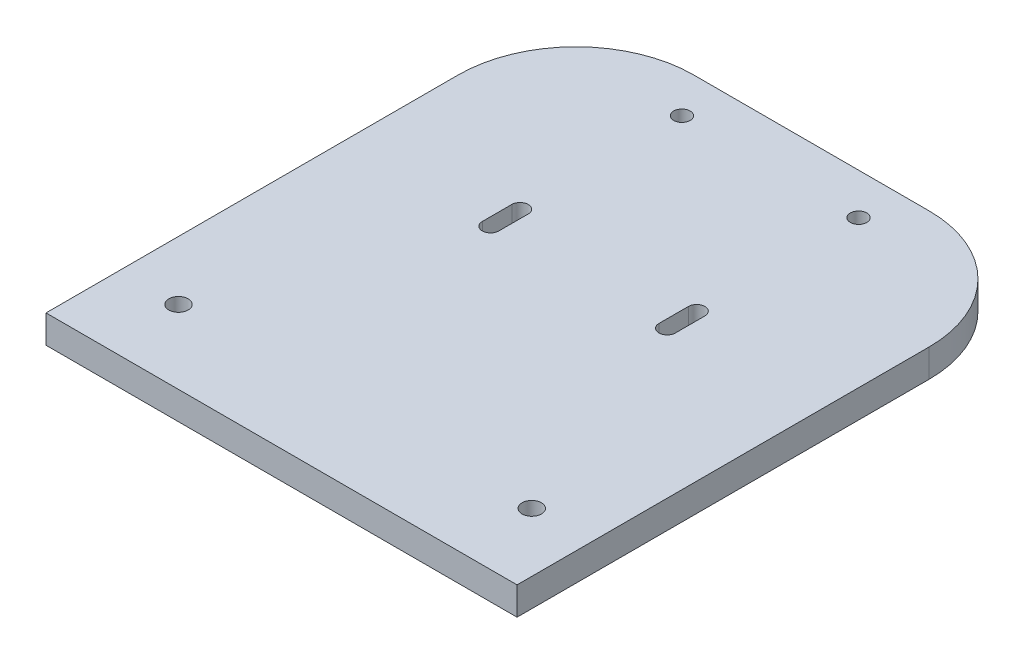
SolidWorks part; units mm, degrees
ref_plane "Front Plane" through (0, 0, 0) normal (0, 0, 1) x (1, 0, 0)
ref_plane "Top Plane" through (0, 0, 0) normal (0, 1, 0) x (1, 0, 0)
ref_plane "Right Plane" through (0, 0, 0) normal (1, 0, 0) x (0, 0, -1)
sketch "Sketch1" plane through (0, 0, 0) normal (0, 1, 0) x (1, 0, 0)
  line L1 (0, 0) -> (80, 0)
  line L2 (0, 0) -> (0, 90)
  line L3 (0, 90) -> (80, 90)
  line L4 (80, 0) -> (80, 90)
  dimension "D1" = 90
  dimension "D2" = 80
extrude "Boss-Extrude1" add sketch "Sketch1" along normal blind 4.76
sketch "Sketch2" plane through (0, 4.76, 0) normal (0, 1, 0) x (1, 0, 0)
  line L0 (0, 12.5) -> (80, 12.5) construction
  line L1 (0, 90) -> (0, 0) construction
  line L2 (80, 0) -> (80, 90) construction
  line L3 (0, 0) -> (80, 0) construction
  line L4 (40, 90) -> (40, 0) construction
  line L5 (80, 90) -> (0, 90) construction
  line L6 (0, 24.3727) -> (0, 25) construction
  line L7 (0, 25) -> (80, 25) construction
  line L8 (0, 68) -> (80, 68) construction
  line L9 (25, 55.5) -> (25, 50.5) construction
  line L10 (26.4, 55.5) -> (26.4, 50.5)
  line L11 (23.6, 55.5) -> (23.6, 50.5)
  line L12 (55, 55.5) -> (55, 50.5) construction
  line L13 (53.6, 55.5) -> (53.6, 50.5)
  line L14 (56.4, 55.5) -> (56.4, 50.5)
  circle A0 centre (10, 12.5) radius 1.65
  circle A1 centre (70, 12.5) radius 1.65
  circle A2 centre (25, 83) radius 1.4
  circle A3 centre (55, 83) radius 1.4
  arc A4 (26.4, 55.5) -> (23.6, 55.5) centre (25, 55.5) ccw
  arc A5 (23.6, 50.5) -> (26.4, 50.5) centre (25, 50.5) ccw
  arc A6 (53.6, 55.5) -> (56.4, 55.5) centre (55, 55.5) cw
  arc A7 (56.4, 50.5) -> (53.6, 50.5) centre (55, 50.5) cw
  point P27 (25, 53)
  point P34 (55, 53)
  dimension "D2" = 3.3
  dimension "D6" = 2.8
  dimension "D9" = 1.4
  dimension "D1" = 12.5
  dimension "D3" = 30
  dimension "D4" = 12.5
  dimension "D5" = 22
  dimension "D7" = 15
  dimension "D8" = 15
  dimension "D10" = 5
  dimension "D11" = 15
extrude "Cut-Extrude1" cut sketch "Sketch2" against normal through all
fillet "Fillet1" radius 20 2 edges at (80, 2.38, -90) (0, 2.38, -90)
equation "\"Change based on what software wants\"= 90"
equation "\"D1@Sketch1\"= \"Change based on what software wants\""
